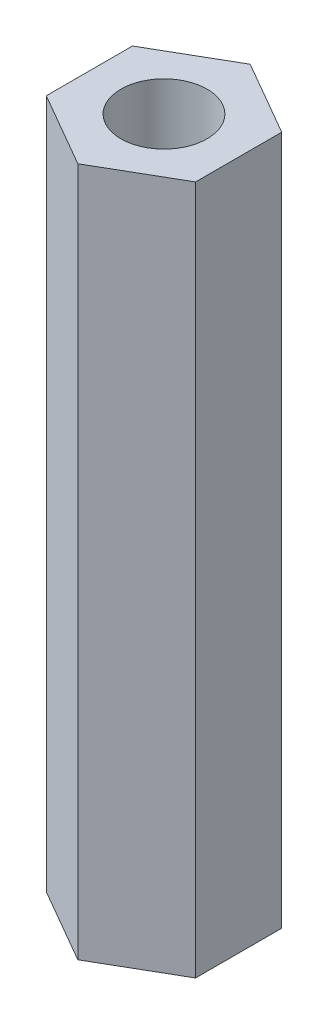
SolidWorks part; units mm, degrees
ref_plane "Face" through (0, 0, 0) normal (0, 0, 1) x (1, 0, 0)
ref_plane "Dessus" through (0, 0, 0) normal (0, 1, 0) x (1, 0, 0)
ref_plane "Droite" through (0, 0, 0) normal (1, 0, 0) x (0, 0, -1)
sketch "Esquisse1" plane through (0, 0, 0) normal (0, 1, 0) x (1, 0, 0)
  line L0 (0, 0) -> (0, 5.5688) construction
  line L1 (0, 5) -> (-4.3301, 2.5)
  line L2 (-4.3301, 2.5) -> (-4.3301, -2.5)
  line L3 (-4.3301, -2.5) -> (0, -5)
  line L4 (0, -5) -> (4.3301, -2.5)
  line L5 (4.3301, -2.5) -> (4.3301, 2.5)
  line L6 (4.3301, 2.5) -> (0, 5)
  circle A0 centre (0, 0) radius 4.3301 construction
  circle A1 centre (0, 0) radius 2.5
  dimension "D1" = 10
  dimension "D2" = 5
extrude "Extrusion1" add sketch "Esquisse1" along normal blind 40
